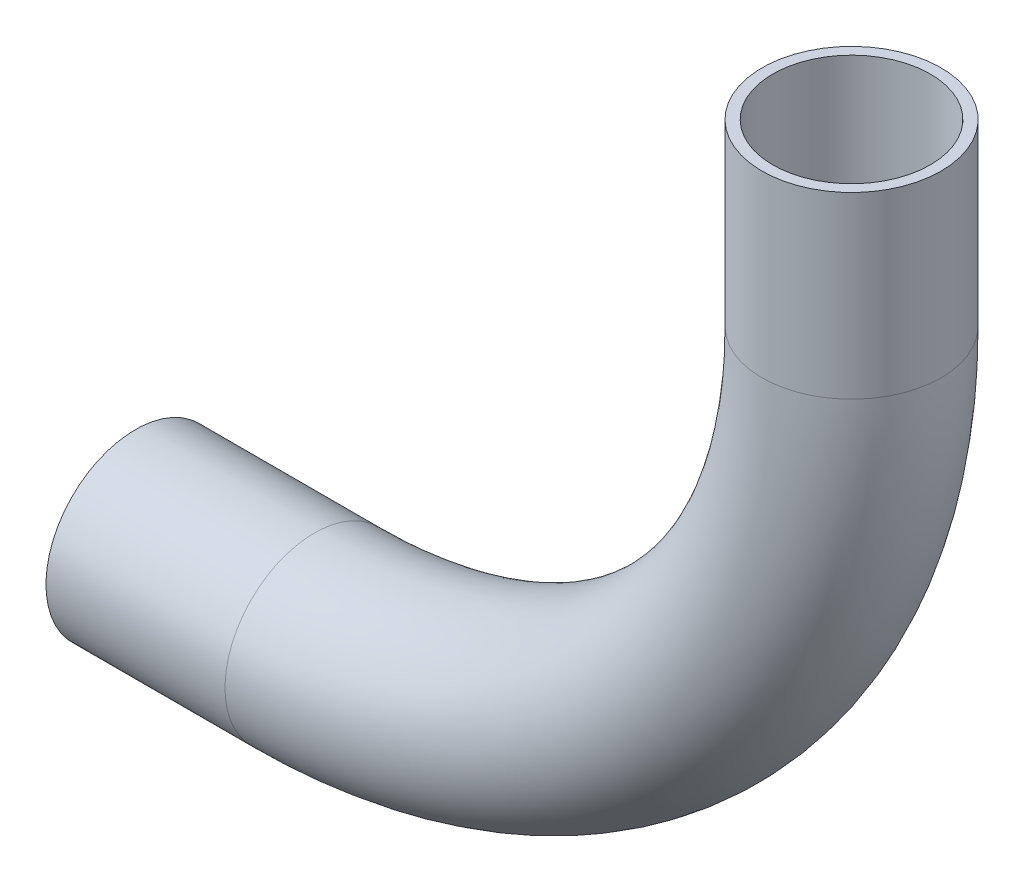
SolidWorks part; units mm, degrees
ref_plane "Front Plane" through (0, 0, 0) normal (0, 0, 1) x (1, 0, 0)
ref_plane "Top Plane" through (0, 0, 0) normal (0, 1, 0) x (1, 0, 0)
ref_plane "Right Plane" through (0, 0, 0) normal (1, 0, 0) x (0, 0, -1)
sketch "Sketch1" plane through (0, 0, 0) normal (0, 0, 1) x (1, 0, 0)
  line L0 (51.1289, 36.3501) -> (51.1289, 23.6501)
  line L1 (13.0289, -14.4499) -> (0.3289, -14.4499)
  arc A0 (51.1289, 23.6501) -> (13.0289, -14.4499) centre (13.0289, 23.6501) cw
  dimension "D1" = 38.1
  dimension "D2" = 12.7
  dimension "D3" = 12.7
  dimension "D4" = 90
ref_plane "Plane1" through (51.1289, 36.3501, 0) normal (0, -1, 0) x (0, 0, -1)
sketch "Sketch2" plane through (51.1289, 36.3501, 0) normal (0, -1, 0) x (0, 0, -1)
  line L0 (0, 0) -> (0, -38.1) construction
  circle A0 centre (0, 0) radius 6.35
  circle A1 centre (0, 0) radius 5.588
  dimension "D1" = 11.176
  dimension "D2" = 12.7
sweep "Sweep1" add profiles "Sketch2" path "Sketch1"
